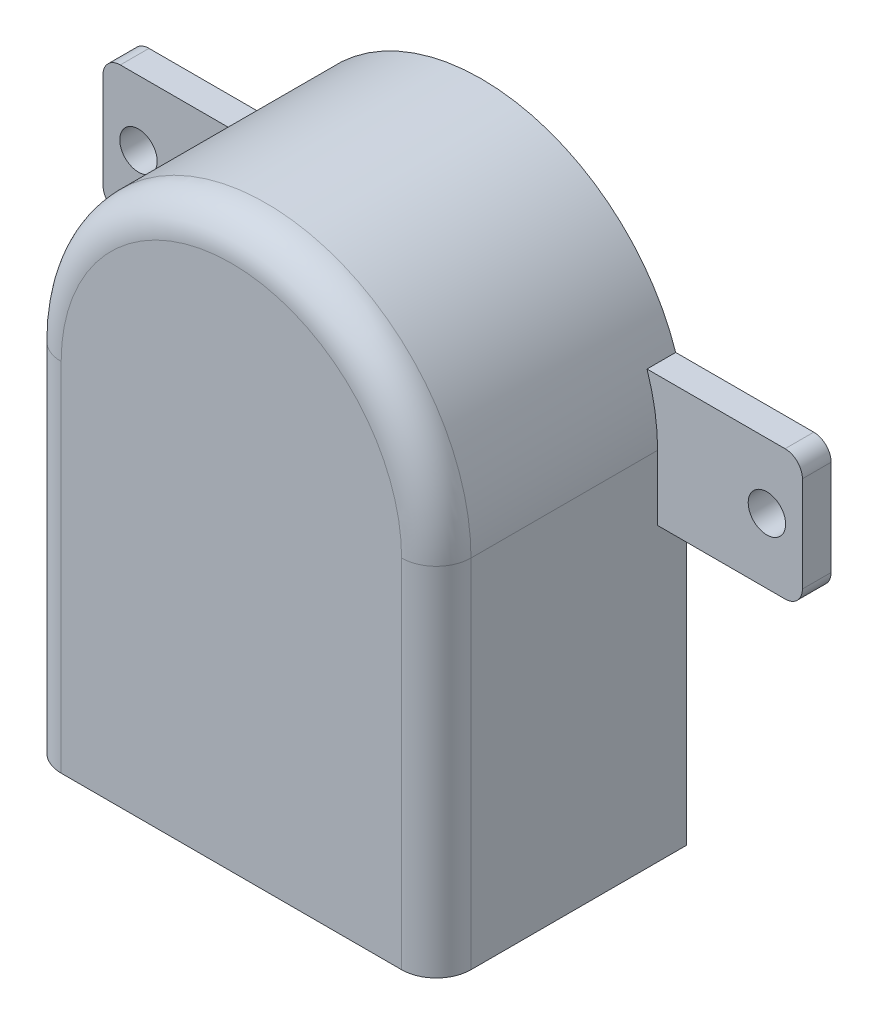
SolidWorks part; units mm, degrees
ref_plane "Front Plane" through (0, 0, 0) normal (0, 0, 1) x (1, 0, 0)
ref_plane "Top Plane" through (0, 0, 0) normal (0, 1, 0) x (1, 0, 0)
ref_plane "Right Plane" through (0, 0, 0) normal (1, 0, 0) x (0, 0, -1)
sketch "Sketch1" plane through (0, 0, 0) normal (0, 0, 1) x (1, 0, 0)
  line L0 (0, 0) -> (0, -17.9603) construction
  line L1 (15, 0) -> (15, -26.1)
  line L2 (-15, 0) -> (-15, -26.1)
  line L3 (-15, -26.1) -> (15, -26.1)
  arc A0 (15, 0) -> (-15, 0) centre (0, 0) ccw
  point P3 (0, -13.05)
  dimension "D2" = 15
  dimension "D1" = 26.1
extrude "Boss-Extrude1" add sketch "Sketch1" along normal blind 18.3
fillet "Fillet1" radius 2.54 3 edges at (15, -13.05, 18.3) (0, 15, 18.3) (-15, -13.05, 18.3)
sketch "Sketch2" plane through (0, 0, 0) normal (0, 0, -1) x (-1, 0, 0)
  line L1 (12.4612, -4.765) -> (25.6, -4.765)
  line L2 (12.4612, -4.765) -> (12.4612, 4.765)
  line L3 (12.4612, 4.765) -> (25.6, 4.765)
  line L4 (25.6, -4.765) -> (25.6, 4.765)
  line L6 (-12.4612, -4.765) -> (-25.6, -4.765)
  line L7 (-12.4612, -4.765) -> (-12.4612, 4.765)
  line L8 (-12.4612, 4.765) -> (-25.6, 4.765)
  line L9 (-25.6, -4.765) -> (-25.6, 4.765)
  circle A0 centre (-23, 0) radius 1.37
  circle A1 centre (23, 0) radius 1.37
  dimension "D5" = 2.74
  dimension "D1" = 51.2
  dimension "D2" = 9.53
  dimension "D3" = 4.765
  dimension "D4" = 46
  dimension "D6" = 23
  dimension "D7" = 4.765
extrude "Boss-Extrude2" add sketch "Sketch2" against normal blind 2.1
fillet "Fillet2" radius 1.27 4 edges at (25.6, 4.765, 1.05) (25.6, -4.765, 1.05) (-25.6, -4.765, 1.05) (-25.6, 4.765, 1.05)
sketch "Sketch3" plane through (0, 0, 0) normal (0, 0, -1) x (-1, 0, 0)
  circle A0 centre (0, 0) radius 4
  dimension "D1" = 8
extrude "Cut-Extrude1" cut sketch "Sketch3" against normal blind 14
sketch "Sketch4" plane through (0, -26.1, 0) normal (0, -1, 0) x (1, 0, 0)
  line L0 (-6.7019, 5.13) -> (7.1319, 5.13) construction
  line L1 (-7.25, 9.23) -> (7.25, 9.23)
  line L2 (-7.25, 9.23) -> (-7.25, 2.13)
  line L3 (-7.25, 2.13) -> (7.25, 2.13)
  line L4 (7.25, 9.23) -> (7.25, 2.13)
  line L5 (-5.4, 5.45) -> (-4.76, 5.45)
  line L6 (-5.4, 5.45) -> (-5.4, 4.81)
  line L7 (-5.4, 4.81) -> (-4.76, 4.81)
  line L8 (-4.76, 5.45) -> (-4.76, 4.81)
  line L9 (-2.86, 5.45) -> (-2.22, 5.45)
  line L10 (-2.86, 5.45) -> (-2.86, 4.81)
  line L11 (-2.86, 4.81) -> (-2.22, 4.81)
  line L12 (-2.22, 5.45) -> (-2.22, 4.81)
  line L13 (-0.32, 5.45) -> (0.32, 5.45)
  line L14 (-0.32, 5.45) -> (-0.32, 4.81)
  line L15 (-0.32, 4.81) -> (0.32, 4.81)
  line L16 (0.32, 5.45) -> (0.32, 4.81)
  line L17 (2.22, 5.45) -> (2.86, 5.45)
  line L18 (2.22, 5.45) -> (2.22, 4.81)
  line L19 (2.22, 4.81) -> (2.86, 4.81)
  line L20 (2.86, 5.45) -> (2.86, 4.81)
  line L21 (4.76, 5.45) -> (5.4, 5.45)
  line L22 (4.76, 5.45) -> (4.76, 4.81)
  line L23 (4.76, 4.81) -> (5.4, 4.81)
  line L24 (5.4, 5.45) -> (5.4, 4.81)
  line L25 (-5.08, 5.45) -> (-5.08, 4.81) construction
  line L26 (-2.54, 4.81) -> (-2.54, 5.45) construction
  line L27 (0, 5.45) -> (0, 4.81) construction
  line L28 (2.54, 5.45) -> (2.54, 4.81) construction
  line L29 (5.08, 5.45) -> (5.08, 4.81) construction
  line L30 (-15, 0) -> (15, 0) construction
  line L31 (0, 0) -> (0, 18.3) construction
  line L32 (-12.46, 18.3) -> (12.46, 18.3) construction
  dimension "D1" = 0.32
  dimension "D2" = 0.64
  dimension "D3" = 2.54
  dimension "D4" = 2.54
  dimension "D5" = 2.54
  dimension "D6" = 2.54
  dimension "D7" = 14.5
  dimension "D8" = 7.1
  dimension "D9" = 2.13
  dimension "D10" = 7.25
  dimension "D11" = 3
extrude "Cut-Extrude2" cut sketch "Sketch4" against normal blind 6.35
equation "\"D3@Sketch2\"=\"D2@Sketch2\"/2"
equation "\"D6@Sketch2\"=\"D4@Sketch2\"/2"
equation "\"D1@Sketch4\"=\"D2@Sketch4\"/2"
equation "\"D4@Sketch4\"=\"D3@Sketch4\""
equation "\"D5@Sketch4\"=\"D4@Sketch4\""
equation "\"D6@Sketch4\"=\"D5@Sketch4\""
equation "\"D10@Sketch4\"=\"D7@Sketch4\"/2"
equation "\"D7@Sketch2\"=\"D2@Sketch2\"/2"
